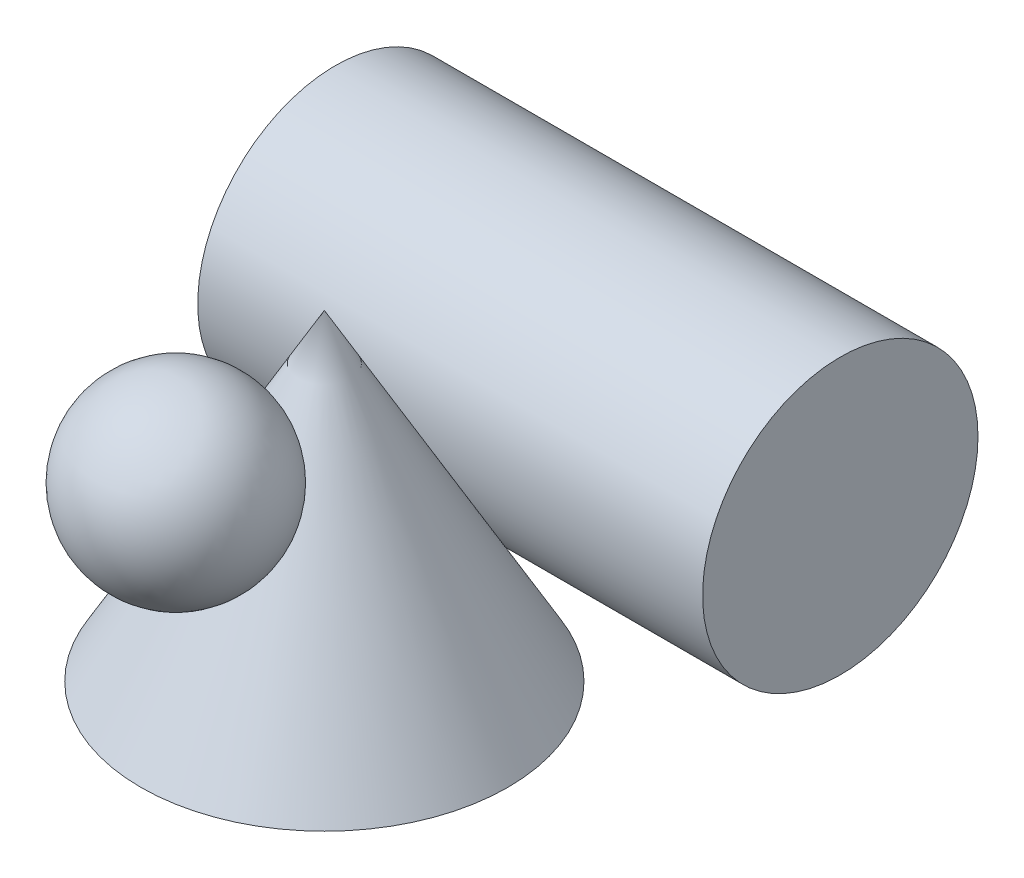
SolidWorks part; units mm, degrees
ref_plane "Front Plane" through (0, 0, 0) normal (0, 0, 1) x (1, 0, 0)
ref_plane "Top Plane" through (0, 0, 0) normal (0, 1, 0) x (1, 0, 0)
ref_plane "Right Plane" through (0, 0, 0) normal (1, 0, 0) x (0, 0, -1)
sketch "Sketch1" plane through (0, 0, 0) normal (0, 0, 1) x (1, 0, 0)
  line L0 (0, 0) -> (40, 0)
  line L1 (40, 0) -> (0, 70)
  line L2 (0, 70) -> (0, 0)
  dimension "D1" = 40
  dimension "D2" = 70
revolve "Revolve1" add sketch "Sketch1" angle 360 about L2
sketch "Sketch2" plane through (0, 0, 0) normal (1, 0, 0) x (0, 0, -1)
  line L0 (40, 0) -> (104.7338, 0) construction
  line L1 (40, 0) -> (0, 70) construction
  circle A0 centre (57.4097, 30) radius 30
  dimension "D1" = 60
extrude "Extrude1" add sketch "Sketch2" against normal mid plane 110 separate body
sketch "Sketch3" plane through (0, 0, 0) normal (1, 0, 0) x (0, 0, -1)
  line L0 (-40, 0) -> (-6.1849, 59.1764) construction
  line L1 (0, 70) -> (-40, 0) construction
  line L2 (-57.3649, 9.9228) -> (-23.5498, 69.0992) construction
  line L3 (0, 0) -> (0, 59.1764) construction
  line L4 (-15, 0) -> (-15, 59.1764) construction
  line L5 (-15, 43.75) -> (-32.3649, 53.6728) construction
  line L6 (-32.3649, 73.6728) -> (-32.3649, 33.6728)
  arc A0 (-32.3649, 33.6728) -> (-32.3649, 73.6728) centre (-32.3649, 53.6728) ccw
  dimension "D1" = 20
  dimension "D2" = 15
revolve "Revolve2" add sketch "Sketch3" angle 360 about L6
